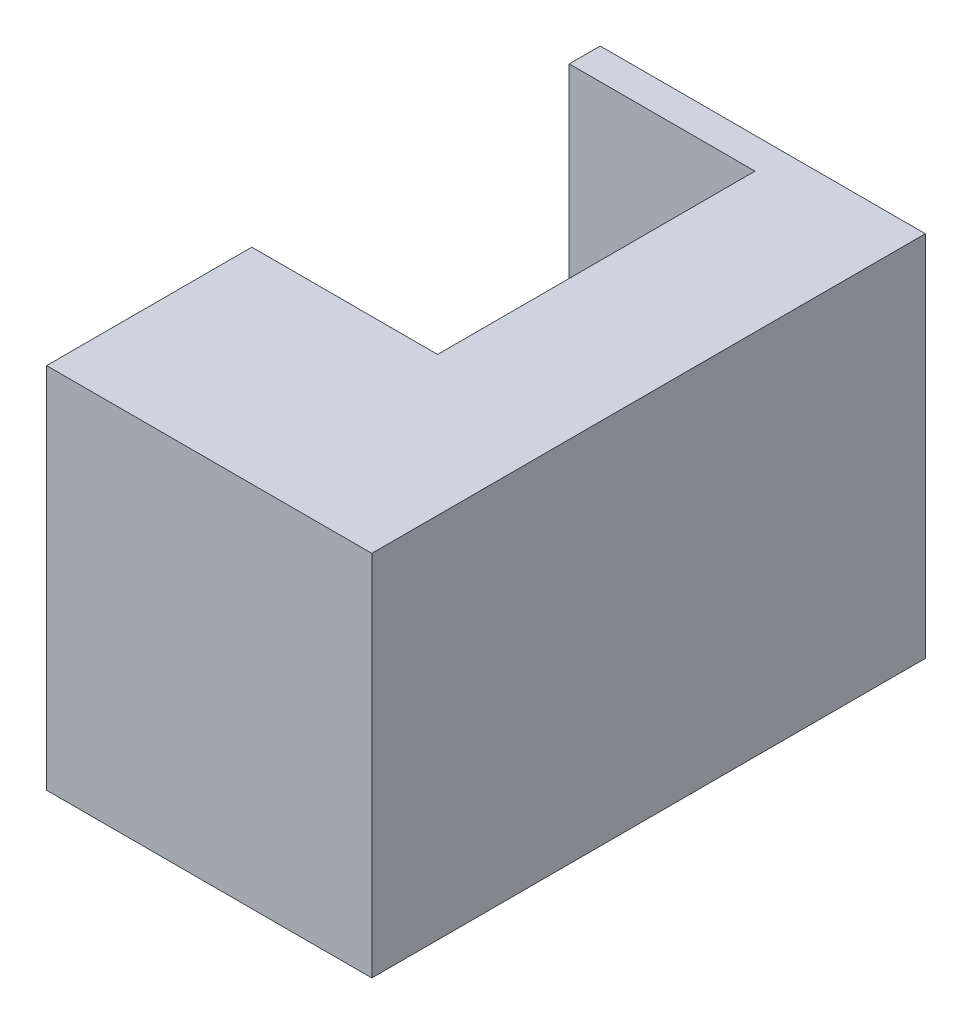
SolidWorks part; units mm, degrees
ref_plane "Front Plane" through (0, 0, 0) normal (0, 0, 1) x (1, 0, 0)
ref_plane "Top Plane" through (0, 0, 0) normal (0, 1, 0) x (1, 0, 0)
ref_plane "Right Plane" through (0, 0, 0) normal (1, 0, 0) x (0, 0, -1)
sketch "Sketch4" plane through (0, 0, 0) normal (1, 0, 0) x (0, 0, -1)
  line L1 (-15.875, 9.875) -> (15.875, 9.875)
  line L2 (-15.875, 9.875) -> (-15.875, -9.875)
  line L3 (-15.875, -9.875) -> (15.875, -9.875)
  line L4 (15.875, 9.875) -> (15.875, -9.875)
  line L5 (-15.875, 9.875) -> (15.875, -9.875) construction
  line L6 (-15.875, -9.875) -> (15.875, 9.875) construction
  point P0 (0, 0)
  dimension "D1" = 31.75
  dimension "D2" = 19.75
extrude "Boss-Extrude1" add sketch "Sketch4" along normal blind 19
shell "Shell1" thickness 2
sketch "Sketch5" plane through (0, 11.875, 0) normal (0, 1, 0) x (1, 0, 0)
  line L0 (0, 15.875) -> (12, 15.875)
  line L1 (0, 17.875) -> (0, -17.875) construction
  line L2 (12, 15.875) -> (12, -4.625)
  line L3 (12, -4.625) -> (0, -4.625)
  line L4 (21, 17.875) -> (0, 17.875) construction
  line L5 (0, -4.625) -> (0, 15.875)
  dimension "D1" = 2
  dimension "D2" = 20.5
  dimension "D3" = 12
extrude "Cut-Extrude1" cut sketch "Sketch5" against normal up to surface (2 mm away) up to face at (9.5, 9.875, 0)
equation "\"terminalRad\"= 3mm"
equation "\"terminalLen\"= 10.5mm"
equation "\"threadlen\"=11"
